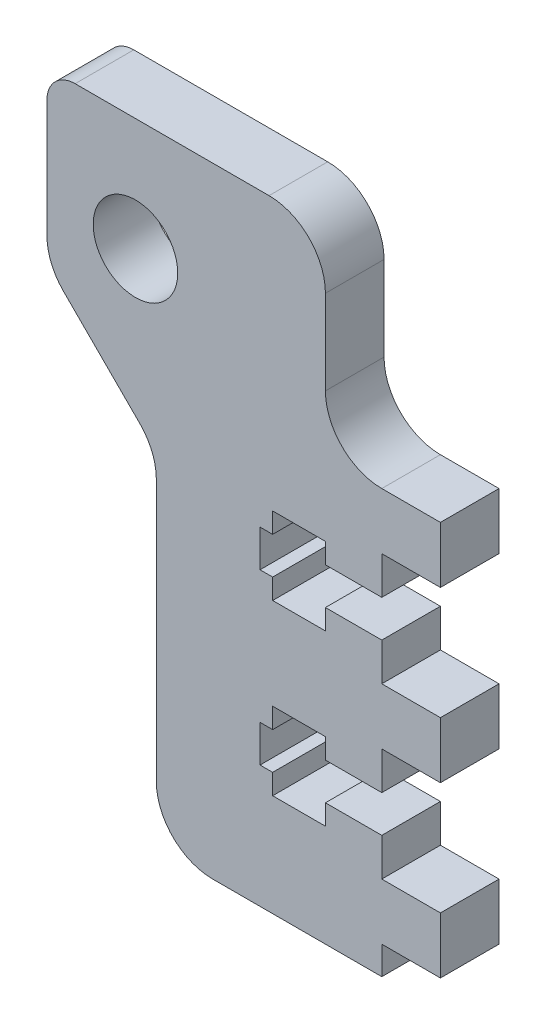
SolidWorks part; units mm, degrees
material "Acrylic (Blue)"
ref_plane "Front Plane" through (0, 0, 0) normal (0, 0, 1) x (1, 0, 0)
ref_plane "Top Plane" through (0, 0, 0) normal (0, 1, 0) x (1, 0, 0)
ref_plane "Right Plane" through (0, 0, 0) normal (1, 0, 0) x (0, 0, -1)
sketch "Sketch1" plane through (0, 0, 0) normal (0, 0, 1) x (1, 0, 0)
  line L0 (0, 0) -> (0, 47.625)
  line L1 (-27.7495, 57.15) -> (-27.7495, 129.438) construction
  line L2 (-37.719, 69.85) -> (-6.35, 69.85)
  line L3 (0, 0) -> (-25.4, 0)
  line L4 (-25.4, 0) -> (-25.4, 38.481)
  line L5 (0, 47.625) -> (-6.35, 47.625)
  line L6 (-37.719, 50.8) -> (-37.719, 69.85)
  line L7 (-37.719, 50.8) -> (-25.4, 38.481)
  line L8 (-6.35, 47.625) -> (-6.35, 69.85)
  circle A0 centre (-27.7495, 57.15) radius 4.7625
  circle A3 centre (-27.7495, 57.15) radius 8.6995 construction
  line B0 (0, 37.0078) -> (-6.35, 37.0078) construction
  line B1 (-6.35, 37.0078) -> (-6.35, 39.2938) construction
  line B2 (-6.35, 39.2938) -> (-12.2936, 39.2938) construction
  line B3 (-12.2936, 39.2938) -> (-12.2936, 37.0078) construction
  line B4 (-12.2936, 37.0078) -> (-13.716, 37.0078) construction
  line B5 (-13.716, 37.0078) -> (-13.716, 32.8422) construction
  line B6 (-13.716, 32.8422) -> (-12.2936, 32.8422) construction
  line B7 (-12.2936, 32.8422) -> (-12.2936, 30.5562) construction
  line B8 (-12.2936, 30.5562) -> (-6.35, 30.5562) construction
  line B9 (-6.35, 30.5562) -> (-6.35, 32.8422) construction
  line B10 (-6.35, 32.8422) -> (0, 32.8422) construction
  line B11 (0, 28.575) -> (6.604, 28.575) construction
  line B12 (6.604, 28.575) -> (6.604, 22.225) construction
  line B13 (6.604, 22.225) -> (0, 22.225) construction
  line B14 (0, 41.275) -> (6.604, 41.275) construction
  line B15 (6.604, 41.275) -> (6.604, 47.625) construction
  line B16 (6.604, 47.625) -> (0, 47.625) construction
  line B17 (6.604, 3.175) -> (0, 3.175) construction
  line B18 (0, 17.9578) -> (-6.35, 17.9578) construction
  line B19 (-6.35, 17.9578) -> (-6.35, 20.2438) construction
  line B20 (-6.35, 20.2438) -> (-12.2936, 20.2438) construction
  line B21 (-12.2936, 20.2438) -> (-12.2936, 17.9578) construction
  line B22 (-12.2936, 17.9578) -> (-13.716, 17.9578) construction
  line B23 (-13.716, 17.9578) -> (-13.716, 13.7922) construction
  line B24 (-13.716, 13.7922) -> (-12.2936, 13.7922) construction
  line B25 (-12.2936, 13.7922) -> (-12.2936, 11.5062) construction
  line B26 (-12.2936, 11.5062) -> (-6.35, 11.5062) construction
  line B27 (-6.35, 11.5062) -> (-6.35, 13.7922) construction
  line B28 (-6.35, 13.7922) -> (0, 13.7922) construction
  line B29 (0, 9.525) -> (6.604, 9.525) construction
  line B30 (6.604, 9.525) -> (6.604, 3.175) construction
  dimension "D3" = 9.525
  dimension "D4" = 57.15
  dimension "D5" = 17.399
  dimension "D2" = 19.05
  dimension "D6" = 25.4
  dimension "D7" = 6.35
  dimension "D8" = 1.27
  dimension "D9" = 19.05
  dimension "D10" = 135
  dimension "D11" = 3.175
  dimension "D12" = 6.35
  dimension "D13" = 69.85
sketch_block_instance "NUT_HOLE_2X-1"
sketch_block "NUT_HOLE_2X" parameters "D1"=6.35, "D2"=4.1656, "D3"=25.4, "D4"=6.604, "D5"=8.7376, "D6"=5.9436, "D7"=6.35, "D8"=20.32, "D9"=2
extrude "Boss-Extrude1" add sketch "Sketch1" along normal blind 6.604
sketch "Sketch2" plane through (0, 0, 6.604) normal (0, 0, 1) x (1, 0, 0)
  line L0 (-12.2936, 37.0078) -> (-13.716, 37.0078) construction
  line L1 (-12.2936, 39.2938) -> (-12.2936, 37.0078) construction
  line L2 (-6.35, 39.2938) -> (-12.2936, 39.2938) construction
  line L3 (-6.35, 37.0078) -> (-6.35, 39.2938) construction
  line L4 (0, 37.0078) -> (-6.35, 37.0078) construction
  line L5 (-6.35, 32.8422) -> (0, 32.8422) construction
  line L6 (-6.35, 30.5562) -> (-6.35, 32.8422) construction
  line L7 (-12.2936, 30.5562) -> (-6.35, 30.5562) construction
  line L8 (-12.2936, 32.8422) -> (-12.2936, 30.5562) construction
  line L9 (-13.716, 32.8422) -> (-12.2936, 32.8422) construction
  line L10 (-13.716, 37.0078) -> (-13.716, 32.8422) construction
  line L11 (-12.2936, 20.2438) -> (-12.2936, 17.9578) construction
  line L12 (-6.35, 20.2438) -> (-12.2936, 20.2438) construction
  line L13 (-12.2936, 17.9578) -> (-13.716, 17.9578) construction
  line L14 (-13.716, 17.9578) -> (-13.716, 13.7922) construction
  line L15 (-13.716, 13.7922) -> (-12.2936, 13.7922) construction
  line L16 (-12.2936, 13.7922) -> (-12.2936, 11.5062) construction
  line L17 (-12.2936, 11.5062) -> (-6.35, 11.5062) construction
  line L18 (-6.35, 11.5062) -> (-6.35, 13.7922) construction
  line L19 (-6.35, 13.7922) -> (0, 13.7922) construction
  line L20 (0, 17.9578) -> (-6.35, 17.9578) construction
  line L21 (-12.2936, 37.0078) -> (-13.716, 37.0078)
  line L22 (-12.2936, 39.2938) -> (-12.2936, 37.0078)
  line L23 (-6.35, 39.2938) -> (-12.2936, 39.2938)
  line L24 (-6.35, 37.0078) -> (-6.35, 39.2938)
  line L25 (0, 37.0078) -> (-6.35, 37.0078)
  line L26 (-6.35, 32.8422) -> (0, 32.8422)
  line L27 (-6.35, 30.5562) -> (-6.35, 32.8422)
  line L28 (-12.2936, 30.5562) -> (-6.35, 30.5562)
  line L29 (-12.2936, 32.8422) -> (-12.2936, 30.5562)
  line L30 (-13.716, 32.8422) -> (-12.2936, 32.8422)
  line L31 (-13.716, 37.0078) -> (-13.716, 32.8422)
  line L32 (-12.2936, 20.2438) -> (-12.2936, 17.9578)
  line L33 (-6.35, 20.2438) -> (-12.2936, 20.2438)
  line L34 (-12.2936, 17.9578) -> (-13.716, 17.9578)
  line L35 (-13.716, 17.9578) -> (-13.716, 13.7922)
  line L36 (-13.716, 13.7922) -> (-12.2936, 13.7922)
  line L37 (-12.2936, 13.7922) -> (-12.2936, 11.5062)
  line L38 (-12.2936, 11.5062) -> (-6.35, 11.5062)
  line L39 (-6.35, 11.5062) -> (-6.35, 13.7922)
  line L40 (-6.35, 13.7922) -> (0, 13.7922)
  line L41 (0, 17.9578) -> (-6.35, 17.9578)
  line L42 (0, 37.0078) -> (0, 32.8422)
  line L43 (0, 17.9578) -> (0, 13.7922)
  line L45 (-6.35, 17.9578) -> (-6.35, 20.2438) construction
  line L46 (-6.35, 17.9578) -> (-6.35, 20.2438)
extrude "Cut-Extrude1" cut sketch "Sketch2" against normal through all
sketch "Sketch3" plane through (0, 0, 6.604) normal (0, 0, 1) x (1, 0, 0)
  line L0 (6.604, 47.625) -> (0, 47.625) construction
  line L1 (6.604, 41.275) -> (6.604, 47.625) construction
  line L2 (0, 41.275) -> (6.604, 41.275) construction
  line L3 (0, 28.575) -> (6.604, 28.575) construction
  line L4 (6.604, 28.575) -> (6.604, 22.225) construction
  line L5 (6.604, 22.225) -> (0, 22.225) construction
  line L6 (0, 9.525) -> (6.604, 9.525) construction
  line L7 (6.604, 9.525) -> (6.604, 3.175) construction
  line L8 (6.604, 3.175) -> (0, 3.175) construction
  line L9 (6.604, 47.625) -> (0, 47.625)
  line L10 (6.604, 41.275) -> (6.604, 47.625)
  line L11 (0, 41.275) -> (6.604, 41.275)
  line L12 (0, 28.575) -> (6.604, 28.575)
  line L13 (6.604, 28.575) -> (6.604, 22.225)
  line L14 (6.604, 22.225) -> (0, 22.225)
  line L15 (0, 9.525) -> (6.604, 9.525)
  line L16 (6.604, 9.525) -> (6.604, 3.175)
  line L17 (6.604, 3.175) -> (0, 3.175)
  line L18 (0, 47.625) -> (0, 41.275)
  line L19 (0, 28.575) -> (0, 22.225)
  line L20 (0, 9.525) -> (0, 3.175)
extrude "Boss-Extrude2" add sketch "Sketch3" against normal up to surface (6.604 mm away) up to face at (-10.7172, 29.1822, 0)
fillet "Fillet1" radius 6.35 5 edges at (-25.4, 0, 3.302) (-25.4, 38.481, 3.302) (-37.719, 50.8, 3.302) (-6.35, 69.85, 3.302) (-6.35, 47.625, 3.302)
fillet "Fillet2" radius 3.175 1 edges at (-37.719, 69.85, 3.302)
other "Move Face1" [suppressed] parameters "D1"=0.0508
